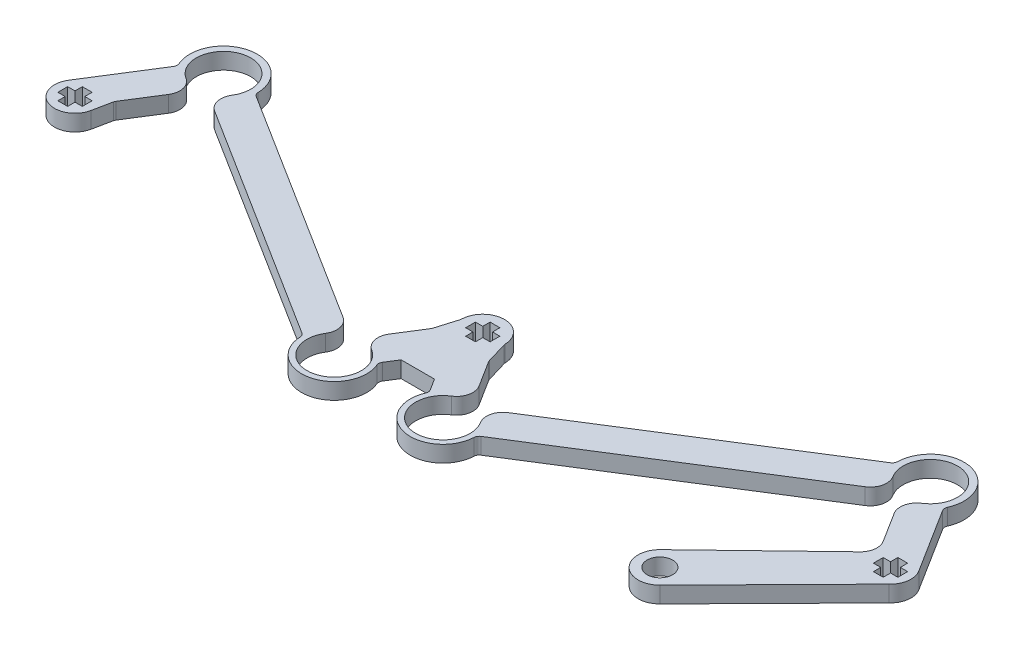
SolidWorks part; units mm, degrees
ref_plane "Front Plane" through (0, 0, 0) normal (0, 0, 1) x (1, 0, 0)
ref_plane "Top Plane" through (0, 0, 0) normal (0, 1, 0) x (1, 0, 0)
ref_plane "Right Plane" through (0, 0, 0) normal (1, 0, 0) x (0, 0, -1)
sketch "Sketch1" plane through (0, 0, 0) normal (0, 1, 0) x (1, 0, 0)
  line L0 (167.744, -82.0717) -> (167.744, -83.8717)
  line L1 (150.3653, -105.9203) -> (172.5302, -85.76) construction
  line L2 (159.5873, -70.6346) -> (166.4873, -81.5897) construction
  line L3 (165.4241, -68.6435) -> (173.1834, -80.9629) construction
  line L4 (153.8041, -66.0043) -> (106.7798, -95.622) construction
  line L5 (158.2082, -70.3214) -> (110.9896, -100.0614) construction
  line L6 (105.4007, -95.3087) -> (100.2128, -87.0717) construction
  line L7 (100.2128, -87.0717) -> (98.994, -82.9717) construction
  line L8 (89.7612, -87.094) -> (90.994, -82.9717) construction
  line L9 (99.6863, -97.4942) -> (98.0646, -94.9194) construction
  line L10 (91.9235, -94.9194) -> (98.0646, -94.9194) construction
  line L11 (90.3017, -97.4942) -> (91.9235, -94.9194) construction
  line L12 (84.5873, -95.3087) -> (89.7612, -87.094) construction
  line L13 (36.184, -66.0043) -> (83.2082, -95.622) construction
  line L14 (31.7798, -70.3214) -> (78.9985, -100.0614) construction
  line L15 (30.4007, -70.6346) -> (24.4225, -80.1263) construction
  line L16 (23.687, -83.7262) -> (24.4225, -80.1263) construction
  line L17 (24.5639, -68.6435) -> (16.8047, -80.9629) construction
  line L18 (172.5302, -85.76) -> (151.6315, -106.9909)
  line L19 (150.3653, -105.9203) -> (150.3621, -105.9233)
  line L20 (159.5873, -70.6346) -> (166.4873, -81.5897)
  line L21 (165.4241, -68.6435) -> (173.1834, -80.9629)
  line L22 (153.8041, -66.0043) -> (106.7798, -95.622)
  line L23 (158.2082, -70.3214) -> (110.9896, -100.0614)
  line L24 (105.4007, -95.3087) -> (100.2128, -87.0717)
  line L25 (100.2128, -87.0717) -> (98.994, -82.9717)
  line L26 (89.7612, -87.094) -> (90.994, -82.9717)
  line L27 (99.6863, -97.4942) -> (98.0646, -94.9194)
  line L28 (91.9235, -94.9194) -> (98.0646, -94.9194)
  line L29 (90.3017, -97.4942) -> (91.9235, -94.9194)
  line L30 (84.5873, -95.3087) -> (89.7612, -87.094)
  line L31 (36.184, -66.0043) -> (83.2082, -95.622)
  line L32 (31.7798, -70.3214) -> (78.9985, -100.0614)
  line L33 (30.4007, -70.6346) -> (24.4225, -80.1263)
  line L34 (23.687, -83.7262) -> (24.4225, -80.1263)
  line L35 (24.5639, -68.6435) -> (16.8047, -80.9629)
  line L36 (166.4873, -81.5897) -> (146.0069, -101.303)
  line L37 (167.744, -83.8717) -> (169.094, -83.8717)
  line L38 (169.094, -83.8717) -> (169.094, -85.2217)
  line L39 (169.094, -85.2217) -> (170.894, -85.2217)
  line L40 (170.894, -85.2217) -> (170.894, -83.8717)
  line L41 (170.894, -83.8717) -> (172.244, -83.8717)
  line L42 (172.244, -83.8717) -> (172.244, -82.0717)
  line L43 (172.244, -82.0717) -> (170.894, -82.0717)
  line L44 (170.894, -82.0717) -> (170.894, -80.7217)
  line L45 (170.894, -80.7217) -> (169.094, -80.7217)
  line L46 (169.094, -80.7217) -> (169.094, -82.0717)
  line L47 (169.094, -82.0717) -> (167.744, -82.0717)
  line L48 (92.744, -82.0717) -> (92.744, -83.8717)
  line L49 (92.744, -83.8717) -> (94.094, -83.8717)
  line L50 (94.094, -83.8717) -> (94.094, -85.2217)
  line L51 (94.094, -85.2217) -> (95.894, -85.2217)
  line L52 (95.894, -85.2217) -> (95.894, -83.8717)
  line L53 (95.894, -83.8717) -> (97.244, -83.8717)
  line L54 (97.244, -83.8717) -> (97.244, -82.0717)
  line L55 (97.244, -82.0717) -> (95.894, -82.0717)
  line L56 (95.894, -82.0717) -> (95.894, -80.7217)
  line L57 (95.894, -80.7217) -> (94.094, -80.7217)
  line L58 (94.094, -80.7217) -> (94.094, -82.0717)
  line L59 (94.094, -82.0717) -> (92.744, -82.0717)
  line L60 (17.744, -82.0717) -> (17.744, -83.8717)
  line L61 (17.744, -83.8717) -> (19.094, -83.8717)
  line L62 (19.094, -83.8717) -> (19.094, -85.2217)
  line L63 (19.094, -85.2217) -> (20.894, -85.2217)
  line L64 (20.894, -85.2217) -> (20.894, -83.8717)
  line L65 (20.894, -83.8717) -> (22.244, -83.8717)
  line L66 (22.244, -83.8717) -> (22.244, -82.0717)
  line L67 (22.244, -82.0717) -> (20.894, -82.0717)
  line L68 (20.894, -82.0717) -> (20.894, -80.7217)
  line L69 (20.894, -80.7217) -> (19.094, -80.7217)
  line L70 (19.094, -80.7217) -> (19.094, -82.0717)
  line L71 (19.094, -82.0717) -> (17.744, -82.0717)
  circle A0 centre (148.7808, -104.1849) radius 2.35 construction
  circle A1 centre (169.994, -82.9717) radius 2.35 construction
  arc A2 (172.5302, -85.76) -> (173.1834, -80.9629) centre (169.994, -82.9717) ccw construction
  arc A3 (159.5873, -70.6346) -> (158.2082, -70.3214) centre (159.994, -65.6512) ccw construction
  arc A4 (165.4241, -68.6435) -> (153.8041, -66.0043) centre (159.994, -65.6512) ccw construction
  arc A5 (105.4007, -95.3087) -> (106.7798, -95.622) centre (104.994, -100.2922) ccw construction
  circle A6 centre (94.994, -82.9717) radius 2.35 construction
  arc A7 (98.994, -82.9717) -> (90.994, -82.9717) centre (94.994, -82.9717) ccw construction
  arc A8 (99.6863, -97.4942) -> (110.9896, -100.0614) centre (104.994, -100.2922) ccw construction
  arc A9 (78.9985, -100.0614) -> (90.3017, -97.4942) centre (84.994, -100.2922) ccw construction
  arc A10 (83.2082, -95.622) -> (84.5873, -95.3087) centre (84.994, -100.2922) ccw construction
  arc A11 (31.7798, -70.3214) -> (30.4007, -70.6346) centre (29.994, -65.6512) ccw construction
  arc A12 (36.184, -66.0043) -> (24.5639, -68.6435) centre (29.994, -65.6512) ccw construction
  circle A13 centre (19.994, -82.9717) radius 2.35 construction
  arc A14 (16.8047, -80.9629) -> (23.687, -83.7262) centre (19.994, -82.9717) ccw construction
  circle A15 centre (148.7808, -104.1849) radius 2.35
  circle A16 centre (169.994, -82.9717) radius 2.35 construction
  arc A17 (172.5302, -85.76) -> (173.1834, -80.9629) centre (169.994, -82.9717) ccw
  arc A18 (159.5873, -70.6346) -> (158.2082, -70.3214) centre (159.994, -65.6512) ccw
  arc A19 (165.4241, -68.6435) -> (153.8041, -66.0043) centre (159.994, -65.6512) ccw
  arc A20 (105.4007, -95.3087) -> (106.7798, -95.622) centre (104.994, -100.2922) ccw
  circle A21 centre (94.994, -82.9717) radius 2.35 construction
  arc A22 (98.994, -82.9717) -> (90.994, -82.9717) centre (94.994, -82.9717) ccw
  arc A23 (99.6863, -97.4942) -> (110.9896, -100.0614) centre (104.994, -100.2922) ccw
  arc A24 (78.9985, -100.0614) -> (90.3017, -97.4942) centre (84.994, -100.2922) ccw
  arc A25 (83.2082, -95.622) -> (84.5873, -95.3087) centre (84.994, -100.2922) ccw
  arc A26 (31.7798, -70.3214) -> (30.4007, -70.6346) centre (29.994, -65.6512) ccw
  arc A27 (36.184, -66.0043) -> (24.5639, -68.6435) centre (29.994, -65.6512) ccw
  circle A28 centre (19.994, -82.9717) radius 2.35 construction
  arc A29 (16.8047, -80.9629) -> (23.687, -83.7262) centre (19.994, -82.9717) ccw
  arc A30 (146.0069, -101.303) -> (151.6315, -106.9909) centre (148.7808, -104.1849) ccw
  circle A31 centre (169.994, -82.9717) radius 2.4233 construction
  circle A32 centre (94.994, -82.9717) radius 2.4233 construction
  circle A33 centre (19.994, -82.9717) radius 2.4233 construction
  dimension "D1" = 8
  dimension "D2" = 1.35
  dimension "D4" = 1.35
  dimension "D3" = 1.8
  dimension "D5" = 1.8
  dimension "D6" = 1.35
  dimension "D7" = 1.8
extrude "Boss-Extrude1" add sketch "Sketch1" along normal blind 3
fillet "Fillet1" radius 3 9 edges at (166.4873, 1.5, 81.5897) (159.5873, 1.5, 70.6346) (158.2082, 1.5, 70.3214) (106.7798, 1.5, 95.622) (105.4007, 1.5, 95.3087) (84.5873, 1.5, 95.3087) (83.2082, 1.5, 95.622) (31.7798, 1.5, 70.3214) (30.4007, 1.5, 70.6346)
fillet "Fillet2" radius 1 13 edges at (100.2128, 1.5, 87.0717) (98.994, 1.5, 82.9717) (90.994, 1.5, 82.9717) (89.7612, 1.5, 87.094) (153.8041, 1.5, 66.0043) (165.4241, 1.5, 68.6435) (110.9896, 1.5, 100.0614) (99.6863, 1.5, 97.4942) (90.3017, 1.5, 97.4942) (78.9985, 1.5, 100.0614) (24.4225, 1.5, 80.1263) (36.184, 1.5, 66.0043) (24.5639, 1.5, 68.6435)
sketch "Sketch2" plane through (0, 3, 0) normal (0, 1, 0) x (1, 0, 0)
  line L1 (150.3621, -105.9233) -> (150.3653, -105.9203)
  line L2 (150.3621, -105.9233) -> (150.3653, -105.9203)
  line L12 (169.094, -82.0717) -> (167.744, -82.0717)
  line L13 (169.094, -80.7217) -> (169.094, -82.0717)
  line L14 (170.894, -80.7217) -> (169.094, -80.7217)
  line L15 (170.894, -82.0717) -> (170.894, -80.7217)
  line L16 (172.244, -82.0717) -> (170.894, -82.0717)
  line L17 (172.244, -83.8717) -> (172.244, -82.0717)
  line L18 (170.894, -83.8717) -> (172.244, -83.8717)
  line L19 (170.894, -85.2217) -> (170.894, -83.8717)
  line L20 (169.094, -85.2217) -> (170.894, -85.2217)
  line L21 (169.094, -83.8717) -> (169.094, -85.2217)
  line L22 (167.744, -83.8717) -> (169.094, -83.8717)
  line L23 (167.744, -82.0717) -> (167.744, -83.8717)
  line L24 (169.094, -82.0717) -> (167.744, -82.0717)
  line L25 (169.094, -80.7217) -> (169.094, -82.0717)
  line L26 (170.894, -80.7217) -> (169.094, -80.7217)
  line L27 (170.894, -82.0717) -> (170.894, -80.7217)
  line L28 (172.244, -82.0717) -> (170.894, -82.0717)
  line L29 (172.244, -83.8717) -> (172.244, -82.0717)
  line L30 (170.894, -83.8717) -> (172.244, -83.8717)
  line L31 (170.894, -85.2217) -> (170.894, -83.8717)
  line L32 (169.094, -85.2217) -> (170.894, -85.2217)
  line L33 (169.094, -83.8717) -> (169.094, -85.2217)
  line L34 (167.744, -83.8717) -> (169.094, -83.8717)
  line L35 (167.744, -82.0717) -> (167.744, -83.8717)
  line L38 (19.094, -82.0717) -> (17.744, -82.0717)
  line L39 (19.094, -80.7217) -> (19.094, -82.0717)
  line L40 (20.894, -80.7217) -> (19.094, -80.7217)
  line L41 (20.894, -82.0717) -> (20.894, -80.7217)
  line L42 (22.244, -82.0717) -> (20.894, -82.0717)
  line L43 (22.244, -83.8717) -> (22.244, -82.0717)
  line L44 (20.894, -83.8717) -> (22.244, -83.8717)
  line L45 (20.894, -85.2217) -> (20.894, -83.8717)
  line L46 (19.094, -85.2217) -> (20.894, -85.2217)
  line L47 (19.094, -83.8717) -> (19.094, -85.2217)
  line L48 (17.744, -83.8717) -> (19.094, -83.8717)
  line L49 (17.744, -82.0717) -> (17.744, -83.8717)
  line L50 (19.094, -82.0717) -> (17.744, -82.0717)
  line L51 (19.094, -80.7217) -> (19.094, -82.0717)
  line L52 (20.894, -80.7217) -> (19.094, -80.7217)
  line L53 (20.894, -82.0717) -> (20.894, -80.7217)
  line L54 (22.244, -82.0717) -> (20.894, -82.0717)
  line L55 (22.244, -83.8717) -> (22.244, -82.0717)
  line L56 (20.894, -83.8717) -> (22.244, -83.8717)
  line L57 (20.894, -85.2217) -> (20.894, -83.8717)
  line L58 (19.094, -85.2217) -> (20.894, -85.2217)
  line L59 (19.094, -83.8717) -> (19.094, -85.2217)
  line L60 (17.744, -83.8717) -> (19.094, -83.8717)
  line L61 (17.744, -82.0717) -> (17.744, -83.8717)
  line L62 (94.094, -82.0717) -> (92.744, -82.0717)
  line L63 (94.094, -80.7217) -> (94.094, -82.0717)
  line L64 (95.894, -80.7217) -> (94.094, -80.7217)
  line L65 (95.894, -82.0717) -> (95.894, -80.7217)
  line L66 (97.244, -82.0717) -> (95.894, -82.0717)
  line L67 (97.244, -83.8717) -> (97.244, -82.0717)
  line L68 (95.894, -83.8717) -> (97.244, -83.8717)
  line L69 (95.894, -85.2217) -> (95.894, -83.8717)
  line L70 (94.094, -85.2217) -> (95.894, -85.2217)
  line L71 (94.094, -83.8717) -> (94.094, -85.2217)
  line L72 (92.744, -83.8717) -> (94.094, -83.8717)
  line L73 (92.744, -82.0717) -> (92.744, -83.8717)
  line L74 (94.094, -82.0717) -> (92.744, -82.0717)
  line L75 (94.094, -80.7217) -> (94.094, -82.0717)
  line L76 (95.894, -80.7217) -> (94.094, -80.7217)
  line L77 (95.894, -82.0717) -> (95.894, -80.7217)
  line L78 (97.244, -82.0717) -> (95.894, -82.0717)
  line L79 (97.244, -83.8717) -> (97.244, -82.0717)
  line L80 (95.894, -83.8717) -> (97.244, -83.8717)
  line L81 (95.894, -85.2217) -> (95.894, -83.8717)
  line L82 (94.094, -85.2217) -> (95.894, -85.2217)
  line L83 (94.094, -83.8717) -> (94.094, -85.2217)
  line L84 (92.744, -83.8717) -> (94.094, -83.8717)
  line L85 (92.744, -82.0717) -> (92.744, -83.8717)
  line L92 (161.7191, -74.0192) -> (165.1857, -79.5232)
  line L93 (164.7277, -83.2834) -> (146.0069, -101.303)
  line L94 (151.6315, -106.9909) -> (172.5302, -85.76)
  line L95 (173.1834, -80.9629) -> (165.723, -69.118)
  line L96 (153.3296, -66.3032) -> (110.1644, -93.4902)
  line L97 (103.269, -91.9241) -> (100.286, -87.188)
  line L98 (100.1736, -86.94) -> (99.0331, -83.1032)
  line L99 (90.9545, -83.1039) -> (89.8004, -86.9632)
  line L100 (89.6884, -87.2096) -> (86.7191, -91.9241)
  line L101 (79.8236, -93.4902) -> (36.6585, -66.3032)
  line L102 (24.265, -69.118) -> (16.8047, -80.9629)
  line L103 (23.687, -83.7262) -> (24.386, -80.3049)
  line L104 (24.5196, -79.9721) -> (28.269, -74.0192)
  line L105 (35.1644, -72.4531) -> (78.5344, -99.7691)
  line L106 (90.594, -97.0302) -> (91.9235, -94.9194)
  line L107 (91.9235, -94.9194) -> (98.0646, -94.9194)
  line L108 (98.0646, -94.9194) -> (99.3941, -97.0302)
  line L109 (111.4536, -99.7691) -> (154.8236, -72.4531)
  line L110 (161.7191, -74.0192) -> (165.1857, -79.5232)
  line L111 (164.7277, -83.2834) -> (146.0069, -101.303)
  line L112 (151.6315, -106.9909) -> (172.5302, -85.76)
  line L113 (173.1834, -80.9629) -> (165.723, -69.118)
  line L114 (153.3296, -66.3032) -> (110.1644, -93.4902)
  line L115 (103.269, -91.9241) -> (100.286, -87.188)
  line L116 (100.1736, -86.94) -> (99.0331, -83.1032)
  line L117 (90.9545, -83.1039) -> (89.8004, -86.9632)
  line L118 (89.6884, -87.2096) -> (86.7191, -91.9241)
  line L119 (79.8236, -93.4902) -> (36.6585, -66.3032)
  line L120 (24.265, -69.118) -> (16.8047, -80.9629)
  line L121 (23.687, -83.7262) -> (24.386, -80.3049)
  line L122 (24.5196, -79.9721) -> (28.269, -74.0192)
  line L123 (35.1644, -72.4531) -> (78.5344, -99.7691)
  line L124 (90.594, -97.0302) -> (91.9235, -94.9194)
  line L125 (91.9235, -94.9194) -> (98.0646, -94.9194)
  line L126 (98.0646, -94.9194) -> (99.3941, -97.0302)
  line L127 (111.4536, -99.7691) -> (154.8236, -72.4531)
  arc A1 (150.3653, -105.9203) -> (150.3621, -105.9233) centre (148.7808, -104.1849) ccw
  arc A2 (150.3653, -105.9203) -> (150.3621, -105.9233) centre (148.7808, -104.1849) ccw
  arc A36 (162.6587, -69.8819) -> (155.7633, -68.3158) centre (159.994, -65.6512) ccw
  arc A37 (162.6587, -69.8819) -> (161.7191, -74.0192) centre (164.2575, -72.4204) ccw
  arc A38 (164.7277, -83.2834) -> (165.1857, -79.5232) centre (162.6472, -81.122) ccw
  arc A39 (146.0069, -101.303) -> (151.6315, -106.9909) centre (148.7808, -104.1849) ccw
  arc A40 (172.5302, -85.76) -> (173.1834, -80.9629) centre (169.994, -82.9717) ccw
  arc A41 (165.656, -68.1775) -> (165.723, -69.118) centre (166.5692, -68.585) ccw
  arc A42 (165.656, -68.1775) -> (153.7963, -65.484) centre (159.994, -65.6512) ccw
  arc A43 (153.3296, -66.3032) -> (153.7963, -65.484) centre (152.7966, -65.4571) ccw
  arc A44 (110.1644, -93.4902) -> (109.2248, -97.6275) centre (111.7633, -96.0287) ccw
  arc A45 (102.3293, -96.0614) -> (109.2248, -97.6275) centre (104.994, -100.2922) ccw
  arc A46 (102.3293, -96.0614) -> (103.269, -91.9241) centre (100.7305, -93.5229) ccw
  arc A47 (100.1736, -86.94) -> (100.286, -87.188) centre (101.1322, -86.6551) ccw
  arc A48 (98.9921, -82.8489) -> (99.0331, -83.1032) centre (99.9917, -82.8183) ccw
  arc A49 (98.9921, -82.8489) -> (90.9959, -82.8482) centre (94.994, -82.9717) ccw
  arc A50 (90.9545, -83.1039) -> (90.9959, -82.8482) centre (89.9964, -82.8174) ccw
  arc A51 (89.6884, -87.2096) -> (89.8004, -86.9632) centre (88.8423, -86.6767) ccw
  arc A52 (86.7191, -91.9241) -> (87.6587, -96.0614) centre (89.2575, -93.5229) ccw
  arc A53 (80.7633, -97.6275) -> (87.6587, -96.0614) centre (84.994, -100.2922) ccw
  arc A54 (80.7633, -97.6275) -> (79.8236, -93.4902) centre (78.2248, -96.0287) ccw
  arc A55 (36.1918, -65.484) -> (36.6585, -66.3032) centre (37.1914, -65.4571) ccw
  arc A56 (36.1918, -65.484) -> (24.3321, -68.1775) centre (29.994, -65.6512) ccw
  arc A57 (24.265, -69.118) -> (24.3321, -68.1775) centre (23.4189, -68.585) ccw
  arc A58 (16.8047, -80.9629) -> (23.687, -83.7262) centre (19.994, -82.9717) ccw
  arc A59 (24.5196, -79.9721) -> (24.386, -80.3049) centre (25.3658, -80.5051) ccw
  arc A60 (28.269, -74.0192) -> (27.3293, -69.8819) centre (25.7305, -72.4204) ccw
  arc A61 (34.2248, -68.3158) -> (27.3293, -69.8819) centre (29.994, -65.6512) ccw
  arc A62 (34.2248, -68.3158) -> (35.1644, -72.4531) centre (36.7633, -69.9147) ccw
  arc A63 (79.0004, -100.5691) -> (78.5344, -99.7691) centre (78.0015, -100.6153) ccw
  arc A64 (79.0004, -100.5691) -> (90.5193, -97.953) centre (84.994, -100.2922) ccw
  arc A65 (90.594, -97.0302) -> (90.5193, -97.953) centre (91.4401, -97.5631) ccw
  arc A66 (99.4688, -97.953) -> (99.3941, -97.0302) centre (98.5479, -97.5631) ccw
  arc A67 (99.4688, -97.953) -> (110.9876, -100.5691) centre (104.994, -100.2922) ccw
  arc A68 (111.4536, -99.7691) -> (110.9876, -100.5691) centre (111.9866, -100.6153) ccw
  arc A69 (154.8236, -72.4531) -> (155.7633, -68.3158) centre (153.2248, -69.9147) ccw
  arc A70 (162.6587, -69.8819) -> (155.7633, -68.3158) centre (159.994, -65.6512) ccw
  arc A71 (162.6587, -69.8819) -> (161.7191, -74.0192) centre (164.2575, -72.4204) ccw
  arc A72 (164.7277, -83.2834) -> (165.1857, -79.5232) centre (162.6472, -81.122) ccw
  arc A73 (146.0069, -101.303) -> (151.6315, -106.9909) centre (148.7808, -104.1849) ccw
  arc A74 (172.5302, -85.76) -> (173.1834, -80.9629) centre (169.994, -82.9717) ccw
  arc A75 (165.656, -68.1775) -> (165.723, -69.118) centre (166.5692, -68.585) ccw
  arc A76 (165.656, -68.1775) -> (153.7963, -65.484) centre (159.994, -65.6512) ccw
  arc A77 (153.3296, -66.3032) -> (153.7963, -65.484) centre (152.7966, -65.4571) ccw
  arc A78 (110.1644, -93.4902) -> (109.2248, -97.6275) centre (111.7633, -96.0287) ccw
  arc A79 (102.3293, -96.0614) -> (109.2248, -97.6275) centre (104.994, -100.2922) ccw
  arc A80 (102.3293, -96.0614) -> (103.269, -91.9241) centre (100.7305, -93.5229) ccw
  arc A81 (100.1736, -86.94) -> (100.286, -87.188) centre (101.1322, -86.6551) ccw
  arc A82 (98.9921, -82.8489) -> (99.0331, -83.1032) centre (99.9917, -82.8183) ccw
  arc A83 (98.9921, -82.8489) -> (90.9959, -82.8482) centre (94.994, -82.9717) ccw
  arc A84 (90.9545, -83.1039) -> (90.9959, -82.8482) centre (89.9964, -82.8174) ccw
  arc A85 (89.6884, -87.2096) -> (89.8004, -86.9632) centre (88.8423, -86.6767) ccw
  arc A86 (86.7191, -91.9241) -> (87.6587, -96.0614) centre (89.2575, -93.5229) ccw
  arc A87 (80.7633, -97.6275) -> (87.6587, -96.0614) centre (84.994, -100.2922) ccw
  arc A88 (80.7633, -97.6275) -> (79.8236, -93.4902) centre (78.2248, -96.0287) ccw
  arc A89 (36.1918, -65.484) -> (36.6585, -66.3032) centre (37.1914, -65.4571) ccw
  arc A90 (36.1918, -65.484) -> (24.3321, -68.1775) centre (29.994, -65.6512) ccw
  arc A91 (24.265, -69.118) -> (24.3321, -68.1775) centre (23.4189, -68.585) ccw
  arc A92 (16.8047, -80.9629) -> (23.687, -83.7262) centre (19.994, -82.9717) ccw
  arc A93 (24.5196, -79.9721) -> (24.386, -80.3049) centre (25.3658, -80.5051) ccw
  arc A94 (28.269, -74.0192) -> (27.3293, -69.8819) centre (25.7305, -72.4204) ccw
  arc A95 (34.2248, -68.3158) -> (27.3293, -69.8819) centre (29.994, -65.6512) ccw
  arc A96 (34.2248, -68.3158) -> (35.1644, -72.4531) centre (36.7633, -69.9147) ccw
  arc A97 (79.0004, -100.5691) -> (78.5344, -99.7691) centre (78.0015, -100.6153) ccw
  arc A98 (79.0004, -100.5691) -> (90.5193, -97.953) centre (84.994, -100.2922) ccw
  arc A99 (90.594, -97.0302) -> (90.5193, -97.953) centre (91.4401, -97.5631) ccw
  arc A100 (99.4688, -97.953) -> (99.3941, -97.0302) centre (98.5479, -97.5631) ccw
  arc A101 (99.4688, -97.953) -> (110.9876, -100.5691) centre (104.994, -100.2922) ccw
  arc A102 (111.4536, -99.7691) -> (110.9876, -100.5691) centre (111.9866, -100.6153) ccw
  arc A103 (154.8236, -72.4531) -> (155.7633, -68.3158) centre (153.2248, -69.9147) ccw
  dimension "D1" = 0
  dimension "D2" = 0
  dimension "D3" = 0
  dimension "D4" = 0
  dimension "D5" = 0
